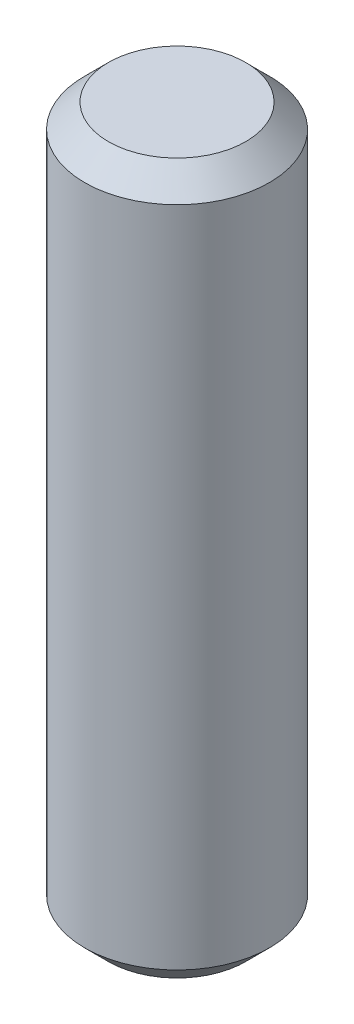
SolidWorks part; units mm, degrees
ref_plane "Front Plane" through (0, 0, 0) normal (0, 0, 1) x (1, 0, 0)
ref_plane "Top Plane" through (0, 0, 0) normal (0, 1, 0) x (1, 0, 0)
ref_plane "Right Plane" through (0, 0, 0) normal (1, 0, 0) x (0, 0, -1)
sketch "Sketch1" plane through (0, 0, 0) normal (0, 1, 0) x (1, 0, 0)
  circle A0 centre (0, 0) radius 3.9
  dimension "D1" = 7.8
extrude "Boss-Extrude1" add sketch "Sketch1" along normal mid plane 30
chamfer "Chamfer1" distance 1 angle 45 2 edges at (0, -15, 3.9) (0, 15, 3.9)
